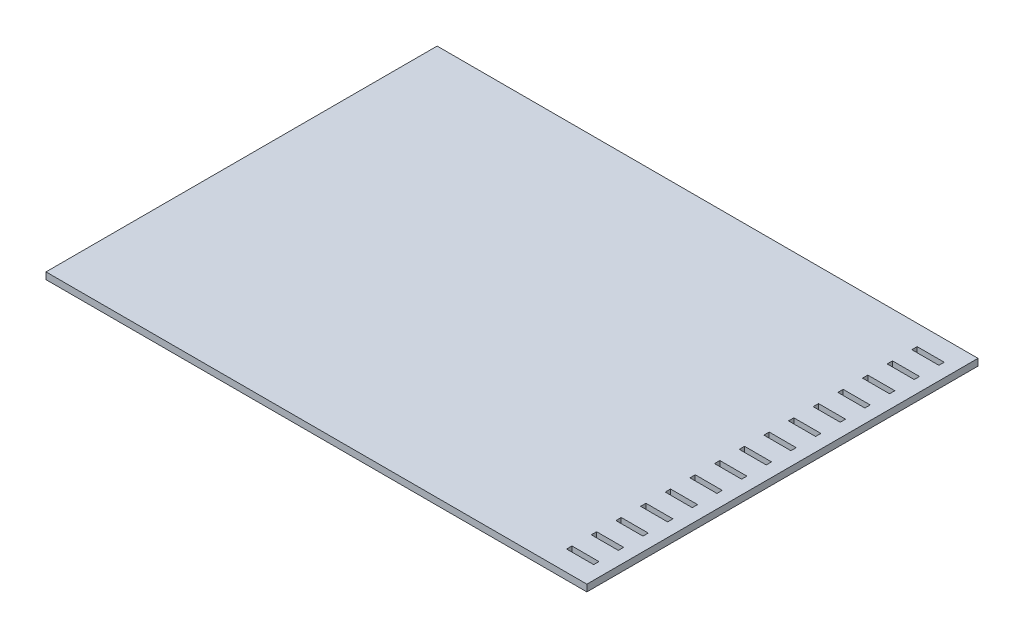
SolidWorks part; units mm, degrees
material "ABS"
ref_plane "Front Plane" through (0, 0, 0) normal (0, 0, 1) x (1, 0, 0)
ref_plane "Top Plane" through (0, 0, 0) normal (0, 1, 0) x (1, 0, 0)
ref_plane "Right Plane" through (0, 0, 0) normal (1, 0, 0) x (0, 0, -1)
sketch "Sketch1" plane through (0, 0, 0) normal (0, 1, 0) x (1, 0, 0)
  line L1 (-66.3921, 26.4776) -> (136.8079, 26.4776)
  line L2 (-66.3921, 26.4776) -> (-66.3921, -120.4614)
  line L3 (-66.3921, -120.4614) -> (136.8079, -120.4614)
  line L4 (136.8079, 26.4776) -> (136.8079, -120.4614)
  dimension "D1" = 203.2
  dimension "D2" = 146.939
extrude "Boss-Extrude1" add sketch "Sketch1" along normal blind 2.54
sketch "Sketch2" plane through (0, 2.54, 0) normal (0, 1, 0) x (0, 0, -1)
  line L14 (-120.4614, 66.3921) -> (-120.4614, -136.8079) construction
  line L15 (-110.8414, -131.7279) -> (-112.8414, -131.7279)
  line L16 (-110.8414, -131.7279) -> (-110.8414, -121.5679)
  line L17 (-110.8414, -121.5679) -> (-112.8414, -121.5679)
  line L18 (-112.8414, -131.7279) -> (-112.8414, -121.5679)
  line L19 (-120.4614, -136.8079) -> (26.4776, -136.8079) construction
  dimension "D1" = 2
  dimension "D2" = 7.62
  dimension "D3" = 5.08
  dimension "D4" = 10.16
extrude "Cut-Extrude1" cut sketch "Sketch2" against normal blind 2.794
pattern_linear "LPattern1" count 15 spacing 9.2642 along (0, 0, -1) of "Cut-Extrude1"
